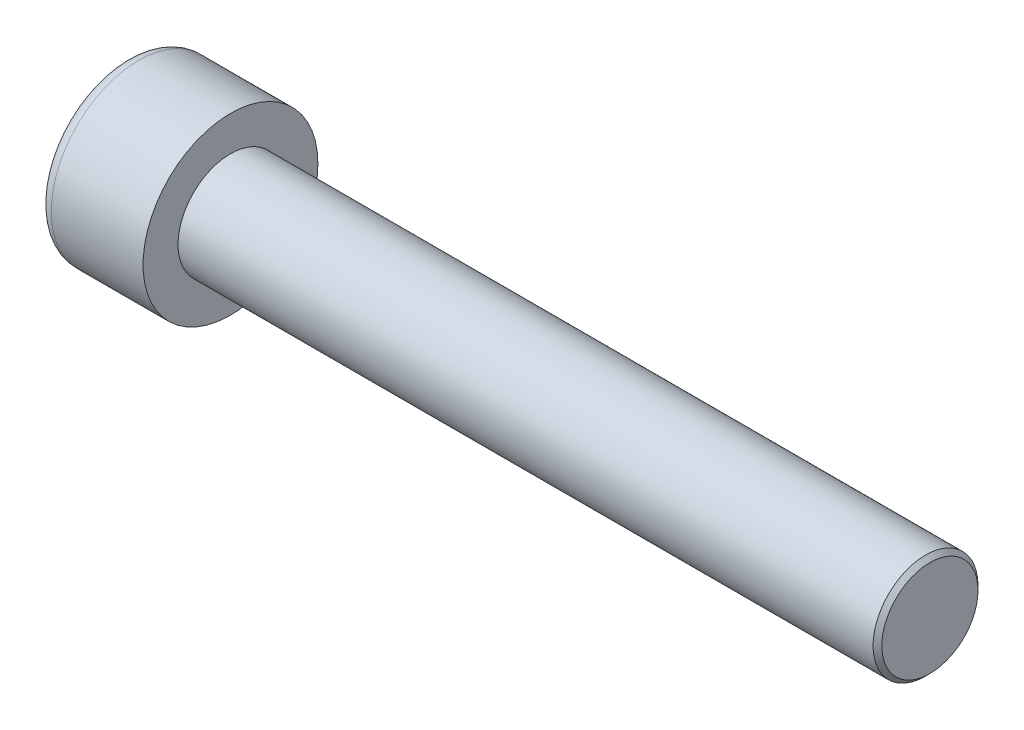
SolidWorks part; units mm, degrees
ref_plane "Front" through (0, 0, 0) normal (0, 0, 1) x (1, 0, 0)
ref_plane "Top" through (0, 0, 0) normal (0, 1, 0) x (1, 0, 0)
ref_plane "Right" through (0, 0, 0) normal (1, 0, 0) x (0, 0, -1)
sketch "Sketch1" plane through (0, 0, 0) normal (1, 0, 0) x (0, 0, -1)
  circle A0 centre (0, 0) radius 5
  dimension "dk" = 10
extrude "BaseHead" add sketch "Sketch1" along normal blind 6
sketch "Sketch2" plane through (6, 0, 0) normal (1, 0, 0) x (0, 0, -1)
  circle A0 centre (0, 0) radius 3
  dimension "d" = 6
extrude "BaseBody" add sketch "Sketch2" along normal blind 40
cosmetic thread "ThreadCosmetic1" parameters "b"=30, "D2"=4.917
sketch "Sketch3" plane through (0, 0, 0) normal (1, 0, 0) x (0, 0, -1)
  line L1 (2.8868, 0) -> (1.4434, 2.5)
  line L2 (1.4434, 2.5) -> (-1.4434, 2.5)
  line L3 (-1.4434, 2.5) -> (-2.8868, 0)
  line L4 (-2.8868, 0) -> (-1.4434, -2.5)
  line L5 (-1.4434, -2.5) -> (1.4434, -2.5)
  line L6 (1.4434, -2.5) -> (2.8868, 0)
  circle A0 centre (0, 0) radius 2.5 construction
  dimension "s" = 5
  dimension "e" = 5.7735
extrude "HexagonSocket" cut sketch "Sketch3" along normal blind 3
sketch "Sketch4" plane through (-4.1961, 0.75, 0) normal (0, 0, 1) x (-1, 0, 0)
  line L0 (-7.1961, 3.25) -> (-8.6395, 0.75)
  line L2 (-8.6395, 0.75) -> (-7.1961, 0.75)
  line L3 (-7.1961, 0.75) -> (-7.1961, 3.25)
  line L4 (-5.0351, 0.75) -> (0.839, 0.75) construction
  line L5 (-50.1961, 0.75) -> (-10.1961, 0.75) construction
  line L6 (-10.1961, 0.75) -> (-4.1961, 0.75) construction
  dimension "m" = 60
revolve "Cut-Revolve1" cut sketch "Sketch4" angle 360 about L4
fillet "HeadFillet" [suppressed] radius 0.25
fillet "TopFillet" radius 0.75 1 edges at (0, 0, -5)
chamfer "Chamfer1" distance 0.25 angle 45 1 edges at (46, 0, -3)
sketch "Sketch5" plane through (0, 0, 0) normal (0, 0, 1) x (1, 0, 0)
  line L0 (45.75, 2.531) -> (46.0208, 3)
  line L1 (46.0208, 3) -> (46.0208, 3.5415)
  line L2 (46.0208, 3.5415) -> (45.4793, 3.5415)
  line L3 (45.4793, 3.5415) -> (45.4793, 3)
  line L4 (45.4793, 3) -> (45.75, 2.531)
  line L5 (0, 0) -> (7.8886, 0) construction
  line L6 (45.75, -3) -> (45.75, 3) construction
  dimension "D1" = 6
  dimension "D2" = 0.5415
revolve "Cut-Revolve10" [suppressed] cut sketch "Sketch5" angle 360 about L5
pattern_linear "LPattern10" [suppressed] count 46 spacing 0.6498 along (1, 0, 0)
equation "\"r1@TopFillet\" = \"d@Sketch2\" / 8"
equation "\"D1@Chamfer1\" = \"r@HeadFillet\""
equation "\"D1@Sketch5\" = \"d@Sketch2\""
equation "\"D2@Sketch5\" =  ( \"d@Sketch2\" - \"D2@ThreadCosmetic1\" )  / 2"
equation "\"D3@LPattern10\" = \"D2@Sketch5\" * 1.2"
equation "\"D1@LPattern10\" = \"b@ThreadCosmetic1\" / \"D3@LPattern10\""
